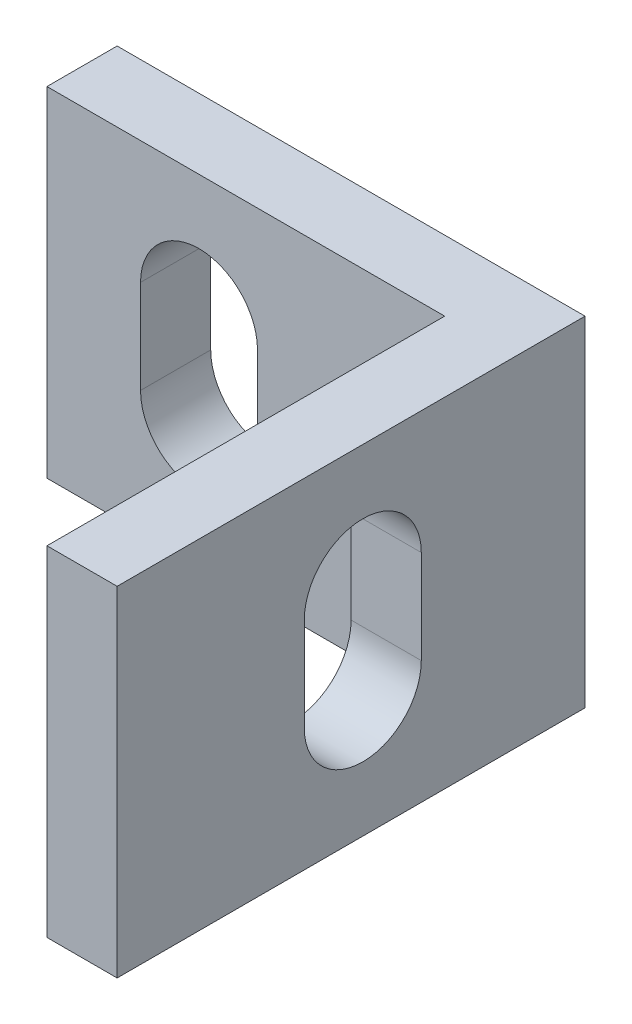
SolidWorks part; units mm, degrees
ref_plane "Front" through (0, 0, 0) normal (0, 0, 1) x (1, 0, 0)
ref_plane "Top" through (0, 0, 0) normal (0, 1, 0) x (1, 0, 0)
ref_plane "Right" through (0, 0, 0) normal (1, 0, 0) x (0, 0, -1)
sketch "Sketch1" plane through (0, 0, 0) normal (0, 1, 0) x (1, 0, 0)
  line L0 (0, 0) -> (0, -17)
  line L1 (0, -17) -> (3, -17)
  line L2 (3, -17) -> (3, 3)
  line L3 (3, 3) -> (-17, 3)
  line L4 (-17, 3) -> (-17, 0)
  line L5 (-17, 0) -> (0, 0)
  point P6 (0.3685, 0)
  point P8 (0, 0)
  dimension "D1" = 20
  dimension "D2" = 3
extrude "Boss-Extrude1" add sketch "Sketch1" along normal mid plane 14.5
sketch "Sketch2" plane through (0, 0, 0) normal (0, 0, 1) x (1, 0, 0)
  line L0 (-10.5, 2) -> (-10.5, -2) construction
  line L1 (-8, 2) -> (-8, -2)
  line L2 (-13, 2) -> (-13, -2)
  line L3 (3, 7.25) -> (3, -7.25) construction
  arc A0 (-8, 2) -> (-13, 2) centre (-10.5, 2) ccw
  arc A1 (-13, -2) -> (-8, -2) centre (-10.5, -2) ccw
  point P2 (-10.5, 0)
  point P9 (0, 0)
  dimension "D1" = 5
  dimension "D2" = 13.5
  dimension "D3" = 4
extrude "Cut-Extrude1" cut sketch "Sketch2" against normal through all both and the other way through all
sketch "Sketch3" plane through (0, 0, 0) normal (1, 0, 0) x (0, 0, -1)
  line L0 (-6.5, 2) -> (-6.5, -2) construction
  line L1 (-4, 2) -> (-4, -2)
  line L2 (-9, 2) -> (-9, -2)
  line L3 (3, 7.25) -> (3, -7.25) construction
  arc A0 (-4, 2) -> (-9, 2) centre (-6.5, 2) ccw
  arc A1 (-9, -2) -> (-4, -2) centre (-6.5, -2) ccw
  point P2 (-6.5, 0)
  point P7 (-4, 0)
  point P10 (0, 0)
  dimension "D1" = 4
  dimension "D2" = 5
  dimension "D3" = 9.5
extrude "Cut-Extrude2" cut sketch "Sketch3" against normal through all both and the other way through all
